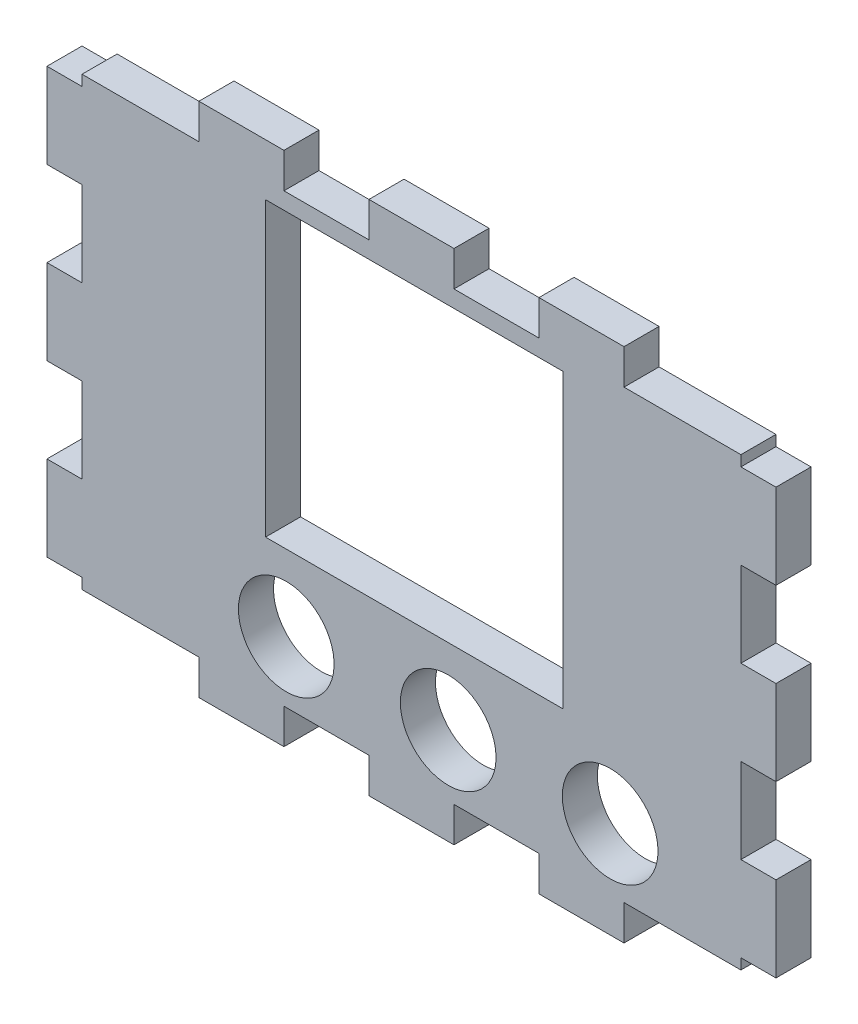
SolidWorks part; units mm, degrees
ref_plane "Plan de face" through (0, 0, 0) normal (0, 0, 1) x (1, 0, 0)
ref_plane "Plan de dessus" through (0, 0, 0) normal (0, 1, 0) x (1, 0, 0)
ref_plane "Plan de droite" through (0, 0, 0) normal (1, 0, 0) x (0, 0, -1)
sketch "Esquisse1" plane through (0, 0, 0) normal (0, 0, 1) x (1, 0, 0)
  line L1 (-31, 21) -> (31, 21)
  line L2 (-31, 21) -> (-31, -21)
  line L3 (-31, -21) -> (31, -21)
  line L4 (31, 21) -> (31, -21)
  line L5 (-31, 21) -> (31, -21) construction
  line L6 (-31, -21) -> (31, 21) construction
  point P0 (0, 0)
  dimension "D1" = 42
  dimension "D2" = 62
extrude "Boss.-Extru.1" add sketch "Esquisse1" along normal blind 3.3
sketch "Esquisse2" plane through (0, 0, 3.3) normal (0, 0, 1) x (1, 0, 0)
  line L0 (31, 21) -> (-31, 21) construction
  line L1 (-4, 24.3) -> (4, 24.3)
  line L2 (-4, 24.3) -> (-4, 21)
  line L3 (-4, 21) -> (4, 21)
  line L4 (4, 24.3) -> (4, 21)
  point P4 (0, 21)
  point P7 (0, 21)
  dimension "D1" = 8
  dimension "D2" = 3.3
extrude "Boss.-Extru.2" add sketch "Esquisse2" against normal blind 3.3
pattern_linear "Répétition linéaire1" count 2 spacing 16 along (-1, 0, 0) count 2 spacing 16 along (1, 0, 0) of "Boss.-Extru.2"
mirror "Symétrie1" about plane through (0, 0, 0) normal (0, 1, 0) of "Répétition linéaire1", "Boss.-Extru.2"
sketch "Esquisse3" plane through (0, 0, 3.3) normal (0, 0, 1) x (1, 0, 0)
  line L0 (-31, 21) -> (-31, -21) construction
  line L1 (-34.3, -4) -> (-31, -4)
  line L2 (-34.3, -4) -> (-34.3, 4)
  line L3 (-34.3, 4) -> (-31, 4)
  line L4 (-31, -4) -> (-31, 4)
  point P4 (-31, 0)
  point P7 (-31, 0)
  dimension "D1" = 8
  dimension "D2" = 3.3
extrude "Boss.-Extru.3" add sketch "Esquisse3" against normal blind 3.3
pattern_linear "Répétition linéaire2" count 2 spacing 16 along (0, 1, 0) count 2 spacing 16 along (0, -1, 0) of "Boss.-Extru.3"
mirror "Symétrie2" about plane through (0, 0, 0) normal (1, 0, 0) of "Répétition linéaire2", "Boss.-Extru.3"
sketch "Esquisse4" plane through (0, 0, 0) normal (0, 0, -1) x (-1, 0, 0)
  line L0 (-18.6975, -15.2187) -> (-3.4575, -15.2187) construction
  line L1 (-14.2677, 19.413) -> (13.7323, 19.413)
  line L2 (-14.2677, 19.413) -> (-14.2677, -8.087)
  line L3 (-14.2677, -8.087) -> (13.7323, -8.087)
  line L4 (13.7323, 19.413) -> (13.7323, -8.087)
  line L5 (-3.4575, -15.2187) -> (11.7825, -15.2187) construction
  circle A0 centre (-18.6975, -15.2187) radius 4.5
  circle A1 centre (-3.4575, -15.2187) radius 4.5
  circle A2 centre (11.7825, -15.2187) radius 4.5
  point P10 (-17.7714, 13.0218)
  point P11 (-15.4768, 18.175)
  point P12 (-14.2677, 19.413)
  dimension "D3" = 9
  dimension "D1" = 28
  dimension "D2" = 27.5
  dimension "D4" = 15.24
extrude "Enlèv. mat.-Extru.2" cut sketch "Esquisse4" against normal through all both and the other way through all
